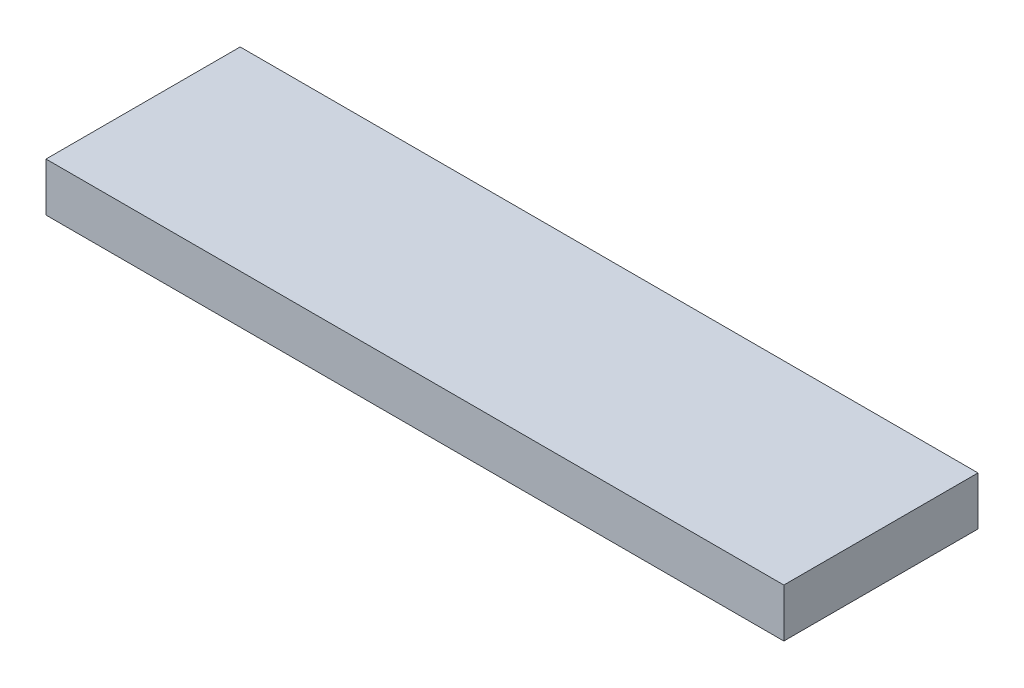
SolidWorks part; units mm, degrees
ref_plane "Front Plane" through (0, 0, 0) normal (0, 0, 1) x (1, 0, 0)
ref_plane "Top Plane" through (0, 0, 0) normal (0, 1, 0) x (1, 0, 0)
ref_plane "Right Plane" through (0, 0, 0) normal (1, 0, 0) x (0, 0, -1)
sketch "Sketch1" plane through (0, 0, 0) normal (0, 1, 0) x (1, 0, 0)
  line L1 (-24.13, 6.35) -> (24.13, 6.35)
  line L2 (-24.13, 6.35) -> (-24.13, -6.35)
  line L3 (-24.13, -6.35) -> (24.13, -6.35)
  line L4 (24.13, 6.35) -> (24.13, -6.35)
  point P4 (0, 6.35)
  point P5 (24.13, 0)
  dimension "D1" = 48.26
  dimension "D2" = 12.7
extrude "Boss-Extrude1" add sketch "Sketch1" along normal blind 3.175
